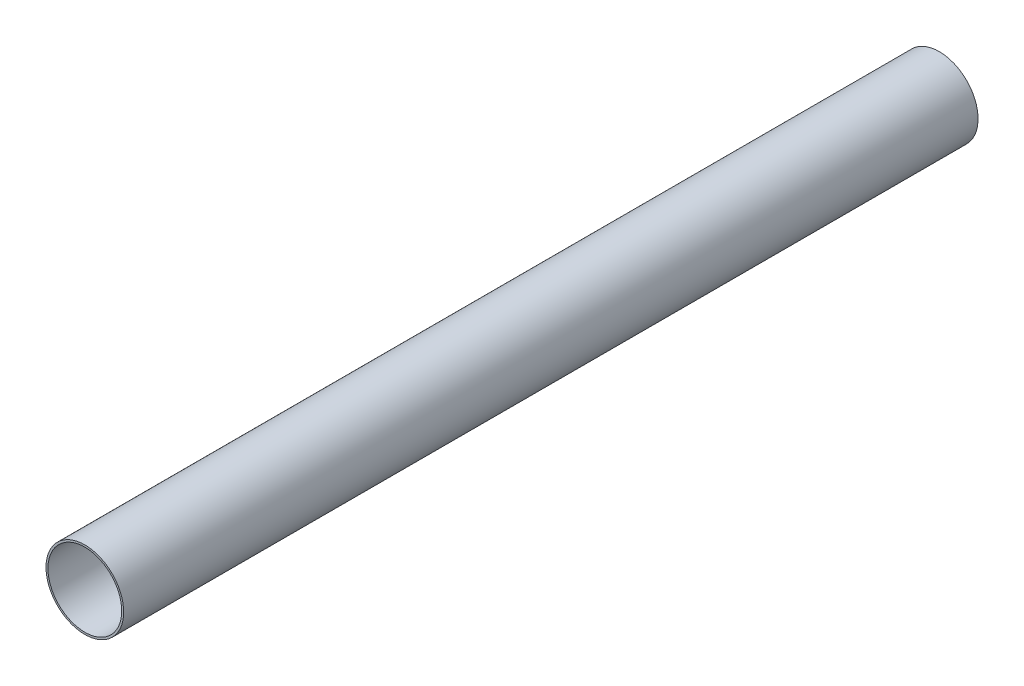
SolidWorks part; units mm, degrees
material "Hexcel AS4C (3000 丝)"
ref_plane "前视基准面" through (0, 0, 0) normal (0, 0, 1) x (1, 0, 0)
ref_plane "上视基准面" through (0, 0, 0) normal (0, 1, 0) x (1, 0, 0)
ref_plane "右视基准面" through (0, 0, 0) normal (1, 0, 0) x (0, 0, -1)
ref_plane "基准面4" through (0, 70.7107, 0) normal (0, -1, 0) x (1, 0, 0)
sketch "草图1" plane through (0, 70.7107, 0) normal (0, -1, 0) x (1, 0, 0)
  line L0 (-60.6857, 181.9) -> (-61.1857, 181.9)
  line L1 (-61.1857, 181.9) -> (-61.1857, -38.1)
  line L2 (-61.1857, -38.1) -> (-60.6857, -38.1)
  line L3 (-60.6857, -38.1) -> (-60.6857, 181.9)
  line L4 (-70.6857, 387.35) -> (-70.6857, -38.1) construction
  line L5 (-61.1857, -38.1) -> (-70.6857, -38.1) construction
  point P6 (0, 0)
revolve "旋转1" add sketch "草图1" angle 360 about L4
